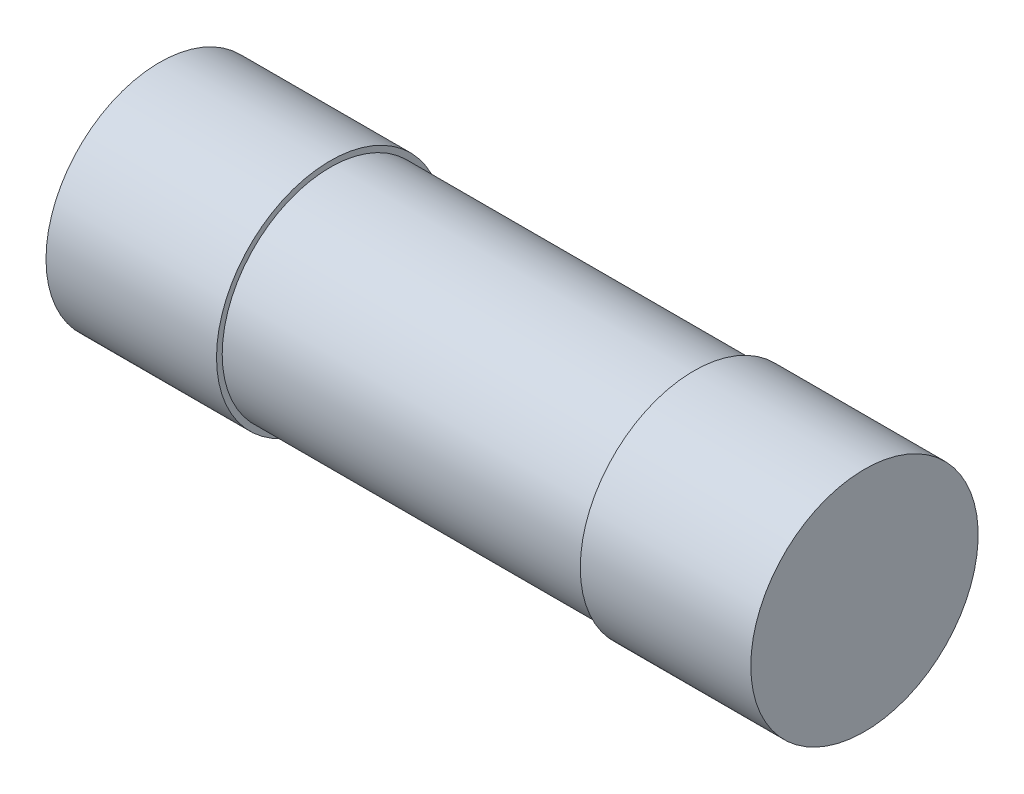
SolidWorks part; units mm, degrees
ref_plane "前视基准面" through (0, 0, 0) normal (0, 0, 1) x (1, 0, 0)
ref_plane "上视基准面" through (0, 0, 0) normal (0, 1, 0) x (1, 0, 0)
ref_plane "右视基准面" through (0, 0, 0) normal (1, 0, 0) x (0, 0, -1)
sketch "草图1" plane through (0, 0, 0) normal (0, 0, 1) x (1, 0, 0)
  line L0 (-40.4651, 0) -> (56.6512, 0) construction
  line L1 (0, 0) -> (0, 10)
  line L2 (15, 9.5) -> (47, 9.5)
  line L3 (47, 9.5) -> (47, 10)
  line L4 (47, 10) -> (62, 10)
  line L10 (62, 0) -> (0, 0)
  line L11 (62, 10) -> (62, 0)
  line L12 (15, 9.5) -> (15, 10)
  line L13 (15, 10) -> (0, 10)
  dimension "D1" = 10
  dimension "D2" = 10
  dimension "D3" = 62
  dimension "D4" = 9.5
  dimension "D5" = 15
  dimension "D6" = 15
revolve "旋转1" add sketch "草图1" angle 360 about L0
ref_plane "基准面1" through (0, 0, 10) normal (0, 0, 1) x (1, 0, 0)
